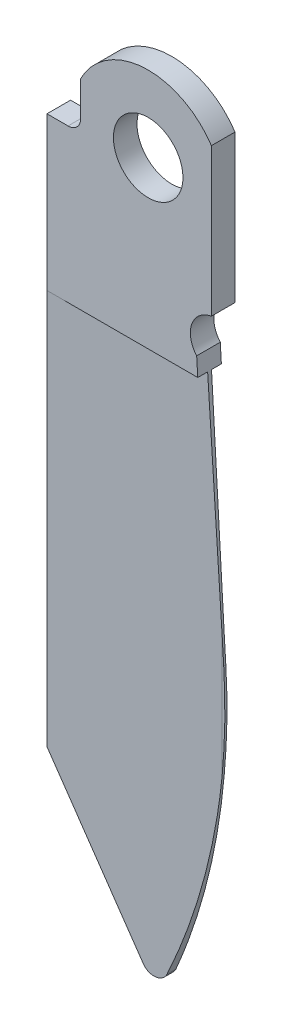
SolidWorks part; units mm, degrees
material "AISI 1045 Steel, cold drawn"
ref_plane "Front Plane" through (0, 0, 0) normal (0, 0, 1) x (1, 0, 0)
ref_plane "Top Plane" through (0, 0, 0) normal (0, 1, 0) x (1, 0, 0)
ref_plane "Right Plane" through (0, 0, 0) normal (1, 0, 0) x (0, 0, -1)
sketch "Sketch1" plane through (0, 0, 0) normal (0, 0, 1) x (1, 0, 0)
  line L0 (18.0689, 40.6551) -> (90.3446, 40.6551) construction
  line L1 (54.8752, 58.9007) -> (54.8752, 25.8807)
  line L3 (54.8752, 25.8807) -> (60.3237, 17.097)
  line L9 (64.8741, 34.7707) -> (63.8921, 50.7808)
  line L12 (64.7812, 53.2914) -> (64.7812, 62.1899)
  line L13 (54.8752, 58.9007) -> (56.1452, 58.9007)
  line L14 (56.9072, 61.7572) -> (56.9072, 59.6627)
  arc A1 (56.1452, 58.9007) -> (56.9072, 59.6627) centre (56.1452, 59.6627) ccw
  arc A3 (64.7812, 62.1899) -> (56.9072, 61.7572) centre (60.9712, 59.6627) ccw
  arc A4 (61.6663, 17.1865) -> (64.8741, 34.7707) centre (27.6062, 32.4847) ccw
  arc A5 (60.3237, 17.097) -> (61.6663, 17.1865) centre (60.9712, 17.4987) ccw
  arc A7 (64.7812, 53.2914) -> (63.8921, 50.7808) centre (65.0352, 51.7887) ccw
  point P3 (0, 0)
  point P4 (0, 0)
  point P10 (0, 0)
  point P13 (62.2006, 60.2261)
  dimension "D1" = 4.572
  dimension "D5" = 6.096
  dimension "D8" = 0.762
  dimension "D9" = 24.892
  dimension "D11" = 27.178
  dimension "D6" = 4.064
  dimension "D4" = 0.762
  dimension "D10" = 1.524
  dimension "D15" = 37.338
  dimension "D19" = 0.762
  dimension "D2" = 7.874
  dimension "D3" = 4.064
  dimension "D7" = 3.81
  dimension "D12" = 33.365
  dimension "D13" = 33.782
extrude "Boss-Extrude1" add sketch "Sketch1" along normal mid plane 1.4224
sketch "Sketch2" plane through (0, 0, 0.7112) normal (0, 0, 1) x (1, 0, 0)
  circle A0 centre (60.9712, 59.6627) radius 2.0955
  dimension "D1" = 4.191
extrude "Cut-Extrude1" cut sketch "Sketch2" against normal through all
sketch "Sketch3" plane through (0, 0, 0) normal (0, 1, 0) x (1, 0, 0)
  line L0 (64.7812, 0.0635) -> (54.8752, 0.7112)
  line L2 (54.8752, -0.7112) -> (54.8752, 0.7112) construction
  line L4 (54.8752, 0.7112) -> (64.7812, 0.7112)
  line L5 (64.7812, 0.7112) -> (64.7812, 0.0635)
  line L6 (54.8752, -0.7112) -> (64.7812, -0.0635)
  line L7 (64.7812, -0.0635) -> (64.7812, -0.7112)
  line L8 (54.8752, -0.7112) -> (64.7812, -0.7112)
  line L10 (64.7812, -0.7112) -> (64.7812, 0.7112) construction
  dimension "D1" = 0.127
  dimension "D2" = 3.741
extrude "Cut-Extrude2" cut sketch "Sketch3" along normal blind 49.6824
sketch "Sketch4" plane through (64.7812, 0, 0) normal (-1, 0, 0) x (0, 0, 1)
  line L16 (0.7112, 36.286) -> (0.0635, 36.286)
  line L21 (0.7112, 36.286) -> (0.7112, 28.9997)
  line L22 (0.7112, 28.9997) -> (0.0635, 28.9997)
  line L23 (0.0635, 36.286) -> (0.0635, 28.9997)
  line L24 (0.7112, 36.286) -> (0.0635, 28.9997) construction
  line L25 (0.7112, 28.9997) -> (0.0635, 36.286) construction
  line L26 (-0.0635, 36.286) -> (-0.7112, 36.286)
  line L27 (-0.0635, 36.286) -> (-0.0635, 28.9997)
  line L28 (-0.0635, 28.9997) -> (-0.7112, 28.9997)
  line L29 (-0.7112, 36.286) -> (-0.7112, 28.9997)
  line L30 (-0.0635, 36.286) -> (-0.7112, 28.9997) construction
  line L31 (-0.0635, 28.9997) -> (-0.7112, 36.286) construction
  point P4 (0.3874, 32.6428)
  point P9 (-0.3873, 32.6428)
extrude "Cut-Extrude4" cut sketch "Sketch4" against normal blind 25.4
